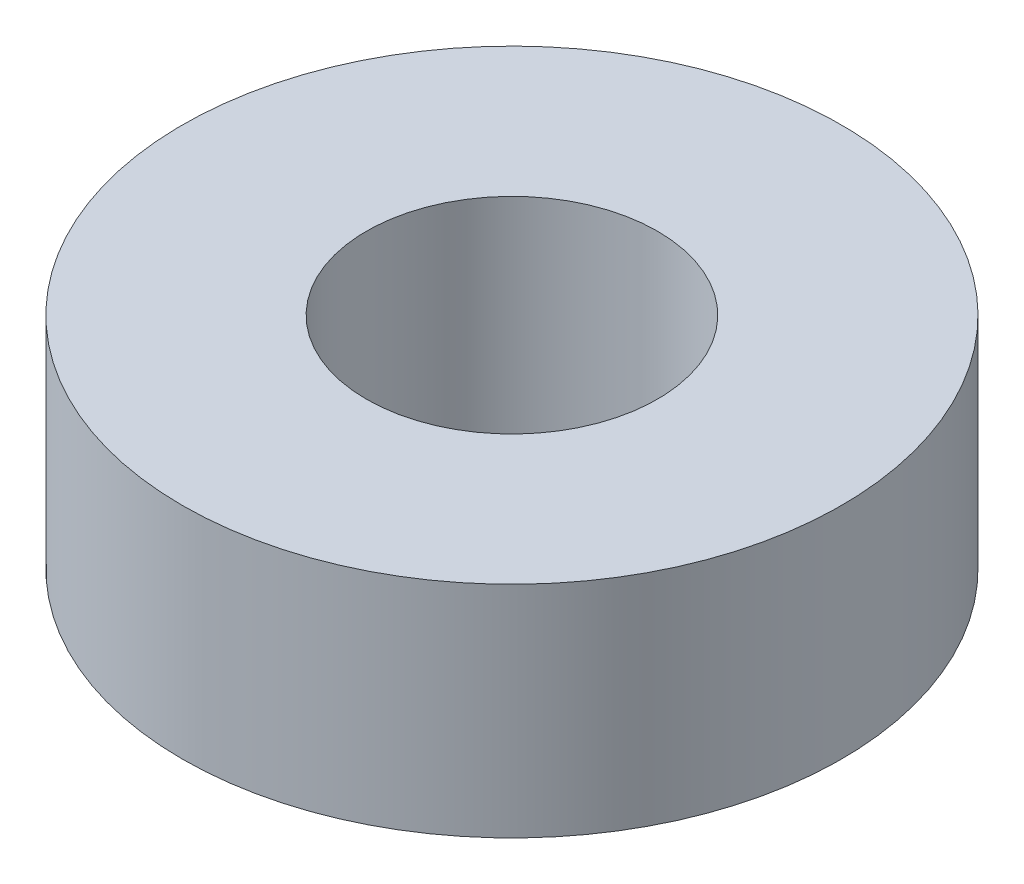
SolidWorks part; units mm, degrees
material "1023 碳钢板 (SS)"
ref_plane "前视基准面" through (0, 0, 0) normal (0, 0, 1) x (1, 0, 0)
ref_plane "上视基准面" through (0, 0, 0) normal (0, 1, 0) x (1, 0, 0)
ref_plane "右视基准面" through (0, 0, 0) normal (1, 0, 0) x (0, 0, -1)
sketch "草图1" plane through (0, 0, 0) normal (0, 1, 0) x (1, 0, 0)
  circle A0 centre (0, 0) radius 6
  circle A1 centre (0, 0) radius 2.65
  dimension "D1" = 5.3
  dimension "D2" = 12
extrude "凸台-拉伸1" add sketch "草图1" along normal blind 4
